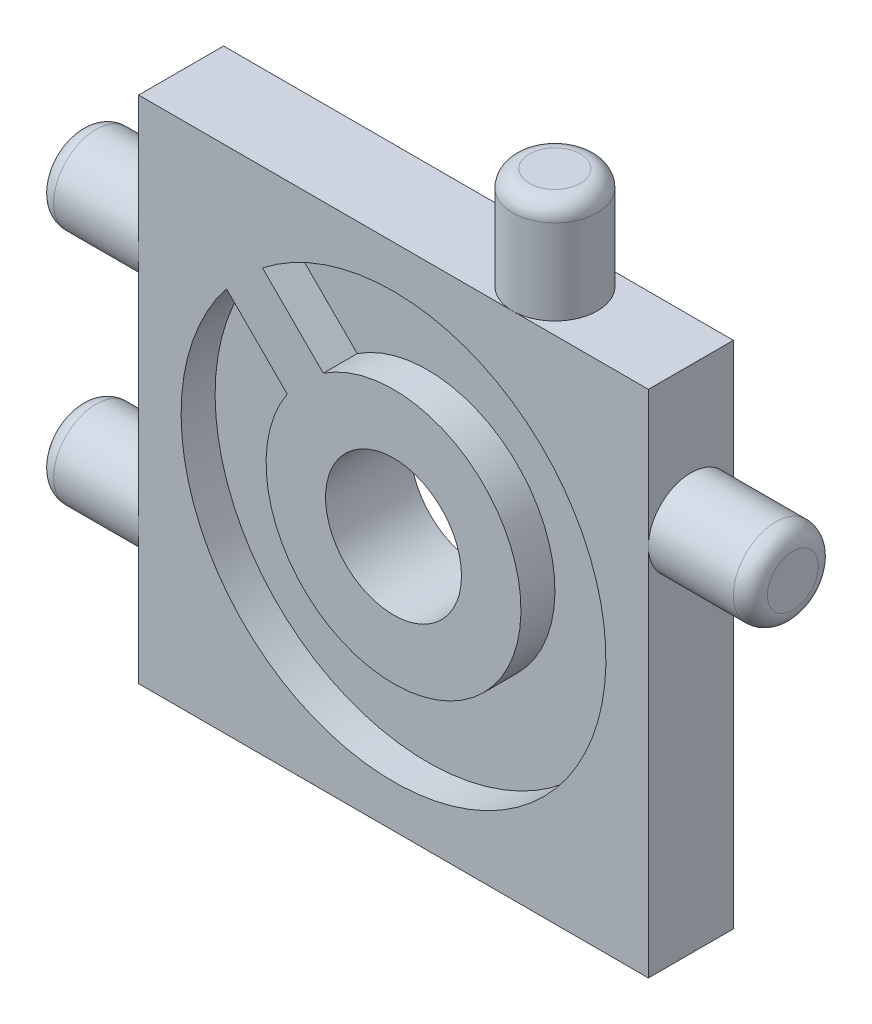
SolidWorks part; units mm, degrees
ref_plane "Plan de face" through (0, 0, 0) normal (0, 0, 1) x (1, 0, 0)
ref_plane "Plan de dessus" through (0, 0, 0) normal (0, 1, 0) x (1, 0, 0)
ref_plane "Plan de droite" through (0, 0, 0) normal (1, 0, 0) x (0, 0, -1)
sketch "Esquisse2" plane through (0, 0, 0) normal (0, 0, 1) x (1, 0, 0)
  line L1 (-15, 15) -> (15, 15)
  line L2 (-15, 15) -> (-15, -15)
  line L3 (-15, -15) -> (15, -15)
  line L4 (15, 15) -> (15, -15)
  line L5 (-15, 15) -> (15, -15) construction
  line L6 (-15, -15) -> (15, 15) construction
  point P0 (0, 0)
  dimension "D1" = 30
  dimension "D2" = 30
extrude "Boss.-Extru.1" add sketch "Esquisse2" along normal blind 5 contours L1 L4 L3 L2
sketch "Esquisse8" plane through (0, 0, 5) normal (0, 0, 1) x (1, 0, 0)
  circle A0 centre (0, 0) radius 12.5
  dimension "D1" = 25
sketch "Esquisse16" plane through (-15, 0, 0) normal (-1, 0, 0) x (0, 0, 1)
  line L0 (2.5, 15) -> (2.5, -15) construction
  line L1 (5, 15) -> (0, 15) construction
  line L2 (5, -15) -> (0, -15) construction
  circle A0 centre (2.5, 7) radius 2.5
  circle A1 centre (2.5, -7) radius 2.5
  dimension "D3" = 5
  dimension "D4" = 5
  dimension "D1" = 8
  dimension "D2" = 8
extrude "Boss.-Extru.7" add sketch "Esquisse16" along normal blind 6
fillet "Congé3" radius 1 2 edges at (-21, -9.5, 2.5) (-21, 4.5, 2.5)
sketch "Esquisse18" plane through (15, 0, 0) normal (1, 0, 0) x (0, 0, -1)
  line L0 (-2.5, -15) -> (-2.5, 15) construction
  line L1 (-5, -15) -> (0, -15) construction
  line L2 (-5, 15) -> (0, 15) construction
  circle A0 centre (-2.5, 7) radius 2.5
  dimension "D2" = 5
  dimension "D1" = 8
extrude "Boss.-Extru.9" add sketch "Esquisse18" along normal blind 6
fillet "Congé5" radius 1 1 edges at (21, 9.5, 2.5)
extrude "Enlèv. mat.-Extru.1" cut sketch "Esquisse8" against normal blind 2 contours A0
sketch "Esquisse19" plane through (0, 0, 3) normal (0, 0, 1) x (1, 0, 0)
  circle A0 centre (0, 0) radius 7.5
  dimension "D1" = 15
extrude "Boss.-Extru.10" add sketch "Esquisse19" along normal blind 2
sketch "Esquisse31" plane through (0, 0, 3) normal (0, 0, 1) x (1, 0, 0)
  line L0 (-15, 15) -> (15, -15) construction
  line L1 (15, 15) -> (-15, -15) construction
  line L2 (-9.8995, 7.7782) -> (-7.7782, 9.8995)
  line L3 (-9.8995, 7.7782) -> (-5.667, 3.5457)
  line L4 (-7.7782, 9.8995) -> (-3.5457, 5.667)
  line L5 (-5.667, 3.5457) -> (-3.5457, 5.667)
  circle A0 centre (0, 0) radius 12.5 construction
  dimension "D1" = 3
  dimension "D2" = 1.5
sketch "Esquisse33" plane through (0, 0, 5) normal (0, 0, 1) x (1, 0, 0)
  circle A0 centre (0, 0) radius 4
extrude "Enlèv. mat.-Extru.3" cut sketch "Esquisse33" against normal through all
sketch "Esquisse35" plane through (0, 15, 0) normal (0, 1, 0) x (1, 0, 0)
  line L0 (-15, -2.5) -> (15, -2.5) construction
  line L1 (-15, -5) -> (-15, 0) construction
  line L2 (15, -5) -> (15, 0) construction
  circle A0 centre (7, -2.5) radius 2.5
  dimension "D1" = 8
extrude "Boss.-Extru.26" add sketch "Esquisse35" along normal blind 6
fillet "Congé6" radius 1 1 edges at (7, 21, 5)
extrude "Boss.-Extru.27" add sketch "Esquisse31" along normal blind 2 and the other way blind 5.5 contours L3 L5 L4 L2
